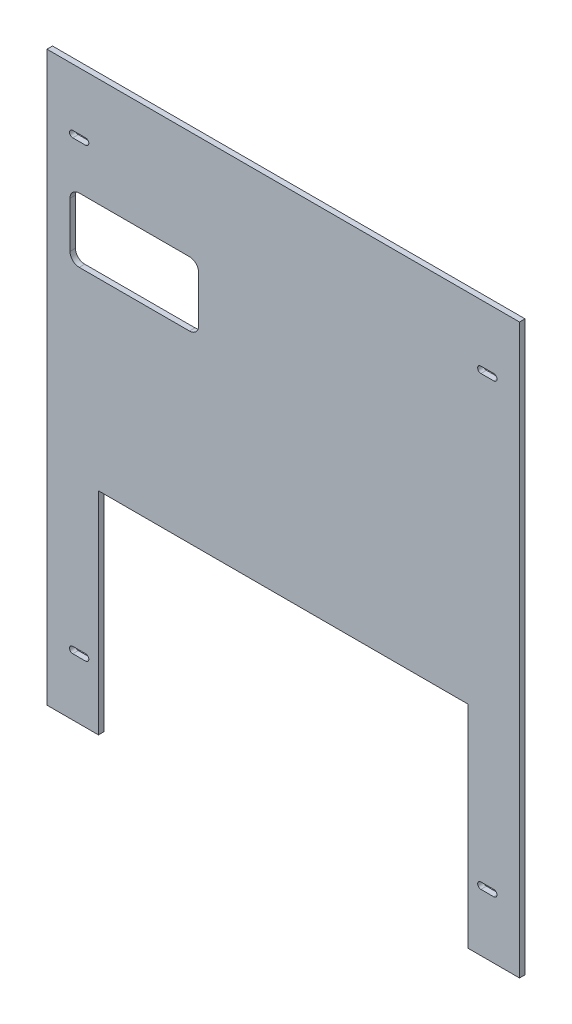
SolidWorks part; units mm, degrees
ref_plane "Plan de face" through (0, 0, 0) normal (0, 0, 1) x (1, 0, 0)
ref_plane "Plan de dessus" through (0, 0, 0) normal (0, 1, 0) x (1, 0, 0)
ref_plane "Plan de droite" through (0, 0, 0) normal (1, 0, 0) x (0, 0, -1)
sketch "Esquisse1" plane through (0, 0, 0) normal (0, 0, 1) x (1, 0, 0)
  line L0 (0, 154.5) -> (0, -154.5) construction
  line L1 (128.5, 154.5) -> (-128.5, 154.5)
  line L2 (128.5, 154.5) -> (128.5, -154.5)
  line L3 (128.5, -154.5) -> (-128.5, -154.5)
  line L4 (-128.5, 154.5) -> (-128.5, -154.5)
  line L5 (128.5, 154.5) -> (-128.5, -154.5) construction
  line L6 (128.5, -154.5) -> (-128.5, 154.5) construction
  line L7 (-111, 121.5) -> (0, 121.5) construction
  line L8 (-128.5, 0) -> (128.5, 0) construction
  line L9 (-114.5, 121.5) -> (-107.5, 121.5) construction
  line L10 (-114.5, 123.25) -> (-107.5, 123.25)
  line L11 (-114.5, 119.75) -> (-107.5, 119.75)
  line L12 (107.5, -121.5) -> (114.5, -121.5) construction
  line L13 (107.5, -119.75) -> (114.5, -119.75)
  line L14 (107.5, -123.25) -> (114.5, -123.25)
  line L15 (-114.5, -121.5) -> (-107.5, -121.5) construction
  line L16 (-114.5, -119.75) -> (-107.5, -119.75)
  line L17 (-114.5, -123.25) -> (-107.5, -123.25)
  line L18 (107.5, 121.5) -> (114.5, 121.5) construction
  line L19 (107.5, 123.25) -> (114.5, 123.25)
  line L20 (107.5, 119.75) -> (114.5, 119.75)
  circle A0 centre (-111, 121.5) radius 1.75 construction
  circle A1 centre (111, 121.5) radius 1.75 construction
  circle A2 centre (111, -121.5) radius 1.75 construction
  circle A3 centre (-111, -121.5) radius 1.75 construction
  arc A4 (-114.5, 123.25) -> (-114.5, 119.75) centre (-114.5, 121.5) ccw
  arc A5 (-107.5, 119.75) -> (-107.5, 123.25) centre (-107.5, 121.5) ccw
  arc A6 (107.5, -119.75) -> (107.5, -123.25) centre (107.5, -121.5) ccw
  arc A7 (114.5, -123.25) -> (114.5, -119.75) centre (114.5, -121.5) ccw
  arc A8 (-114.5, -119.75) -> (-114.5, -123.25) centre (-114.5, -121.5) ccw
  arc A9 (-107.5, -123.25) -> (-107.5, -119.75) centre (-107.5, -121.5) ccw
  arc A10 (107.5, 123.25) -> (107.5, 119.75) centre (107.5, 121.5) ccw
  arc A11 (114.5, 119.75) -> (114.5, 123.25) centre (114.5, 121.5) ccw
  point P0 (0, 0)
  point P21 (-111, 121.5)
  point P28 (111, -121.5)
  point P35 (-111, -121.5)
  point P42 (111, 121.5)
  dimension "D3" = 3.5
  dimension "D7" = 1.75
  dimension "D9" = 1.75
  dimension "D11" = 1.75
  dimension "D13" = 1.75
  dimension "D1" = 257
  dimension "D2" = 309
  dimension "D4" = 111
  dimension "D5" = 33
  dimension "D6" = 7
  dimension "D8" = 7
  dimension "D10" = 7
  dimension "D12" = 7
extrude "Boss.-Extru.1" add sketch "Esquisse1" along normal blind 3
sketch "Esquisse2" plane through (0, 0, 3) normal (0, 0, 1) x (1, 0, 0)
  line L0 (-128.5, -154.5) -> (128.5, -154.5) construction
  line L1 (-100.5, -154.5) -> (100.5, -154.5)
  line L2 (-100.5, -154.5) -> (-100.5, -39.5)
  line L3 (-100.5, -39.5) -> (100.5, -39.5)
  line L4 (100.5, -154.5) -> (100.5, -39.5)
  point P6 (0, -154.5)
  point P7 (0, -154.5)
  dimension "D1" = 201
  dimension "D2" = 115
extrude "Enlèv. mat.-Extru.1" cut sketch "Esquisse2" against normal through all
sketch "Esquisse3" plane through (0, 0, 3) normal (0, 0, 1) x (1, 0, 0)
  line L0 (128.5, 154.5) -> (-128.5, 154.5) construction
  line L1 (-111, 60.5) -> (-51, 60.5)
  line L2 (-116, 65.5) -> (-116, 90.5)
  line L3 (-111, 95.5) -> (-51, 95.5)
  line L4 (-46, 65.5) -> (-46, 90.5)
  line L5 (-128.5, 154.5) -> (-128.5, -154.5) construction
  arc A0 (-111, 60.5) -> (-116, 65.5) centre (-111, 65.5) cw
  arc A1 (-51, 60.5) -> (-46, 65.5) centre (-51, 65.5) ccw
  arc A2 (-51, 95.5) -> (-46, 90.5) centre (-51, 90.5) cw
  arc A3 (-116, 90.5) -> (-111, 95.5) centre (-111, 90.5) cw
  point P10 (-116, 60.5)
  point P15 (-46, 95.5)
  point P18 (-116, 95.5)
  dimension "D5" = 5
  dimension "D1" = 94
  dimension "D2" = 70
  dimension "D3" = 12.5
  dimension "D4" = 35
extrude "Enlèv. mat.-Extru.2" cut sketch "Esquisse3" against normal through all
